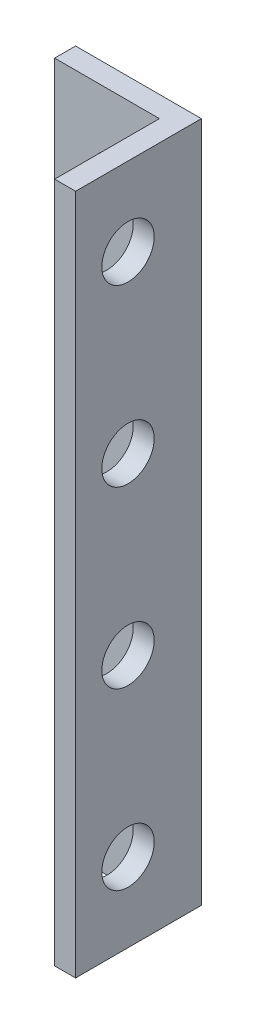
SolidWorks part; units mm, degrees
ref_plane "Front Plane" through (0, 0, 0) normal (0, 0, 1) x (1, 0, 0)
ref_plane "Top Plane" through (0, 0, 0) normal (0, 1, 0) x (1, 0, 0)
ref_plane "Right Plane" through (0, 0, 0) normal (1, 0, 0) x (0, 0, -1)
sketch "Sketch1" plane through (0, 0, 0) normal (0, 0, 1) x (1, 0, 0)
  line L0 (-3.6, 0) -> (3.6, 0) construction
  line L1 (3.6, -19.5) -> (-3.6, -19.5)
  line L2 (3.6, -19.5) -> (3.6, 19.5)
  line L3 (3.6, 19.5) -> (-3.6, 19.5)
  line L4 (-3.6, -19.5) -> (-3.6, 19.5)
  line L5 (3.6, -19.5) -> (-3.6, 19.5) construction
  line L6 (3.6, 19.5) -> (-3.6, -19.5) construction
  circle A0 centre (0, -5) radius 1.5
  circle A1 centre (0, -15) radius 1.5
  circle A2 centre (0, 15) radius 1.5
  circle A3 centre (0, 5) radius 1.5
  point P0 (0, 0)
  dimension "D3" = 3
  dimension "D4" = 3
  dimension "D1" = 7.2
  dimension "D2" = 39
  dimension "D5" = 10
  dimension "D6" = 4.5
extrude "Boss-Extrude1" add sketch "Sketch1" along normal blind 1.2
sketch "Sketch2" plane through (0, 0, 1.2) normal (0, 0, 1) x (1, 0, 0)
  line L0 (-3.6, -19.5) -> (3.6, -19.5) construction
  line L1 (3.6, 19.5) -> (2.4, 19.5)
  line L2 (3.6, 19.5) -> (3.6, -19.5)
  line L3 (3.6, -19.5) -> (2.4, -19.5)
  line L4 (2.4, 19.5) -> (2.4, -19.5)
  dimension "D1" = 1.2
extrude "Boss-Extrude2" add sketch "Sketch2" along normal blind 6
sketch "Sketch3" plane through (2.4, 0, 0) normal (-1, 0, 0) x (0, 0, 1)
  line L0 (7.2, 19.5) -> (1.2, 19.5) construction
  line L1 (1.2, 0) -> (7.2, 0) construction
  line L2 (1.2, 19.5) -> (1.2, -19.5) construction
  line L3 (7.2, 19.5) -> (7.2, -19.5) construction
  circle A0 centre (4.2, 15) radius 1.5
  circle A1 centre (4.2, 5) radius 1.5
  circle A2 centre (4.2, -5) radius 1.5
  circle A3 centre (4.2, -15) radius 1.5
  point P6 (4.2, 19.5)
  dimension "D1" = 3
  dimension "D2" = 3
  dimension "D3" = 10
  dimension "D4" = 4.5
extrude "Cut-Extrude1" cut sketch "Sketch3" against normal up to next
